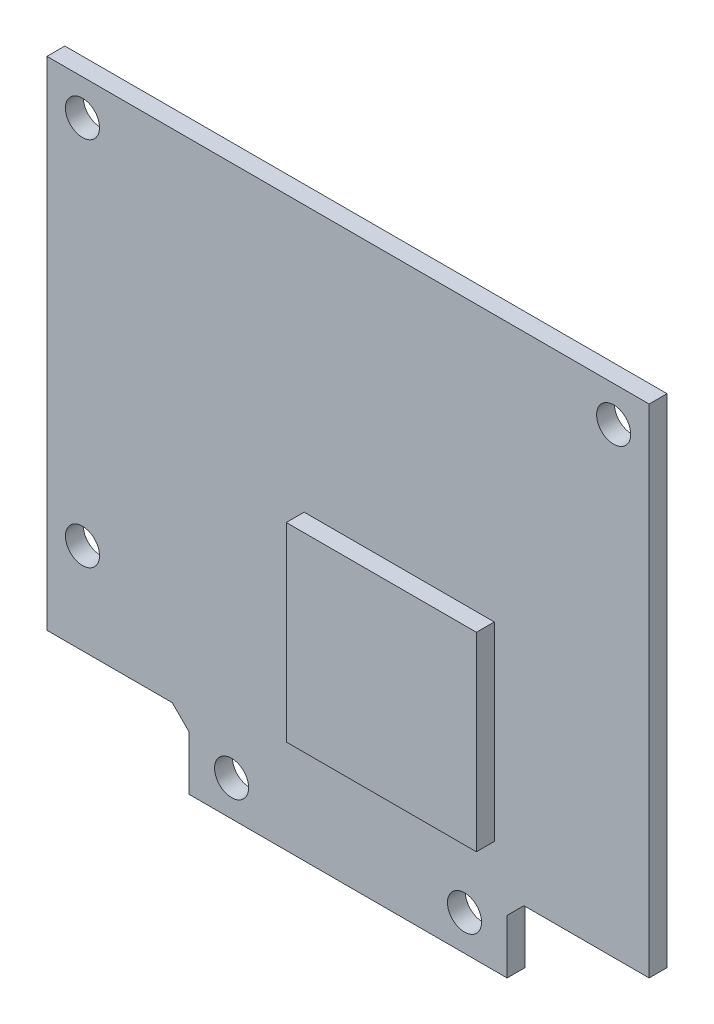
SolidWorks part; units mm, degrees
ref_plane "Plan de face" through (0, 0, 0) normal (0, 0, 1) x (1, 0, 0)
ref_plane "Plan de dessus" through (0, 0, 0) normal (0, 1, 0) x (1, 0, 0)
ref_plane "Plan de droite" through (0, 0, 0) normal (1, 0, 0) x (0, 0, -1)
sketch "PCB_shape" plane through (0, 0, 0) normal (0, 0, 1) x (1, 0, 0)
  line L0 (0, 10.54) -> (0, -40.26) construction
  line L1 (-26.924, 10.54) -> (26.924, 10.54)
  line L2 (-26.924, 10.54) -> (-26.924, -33.91)
  line L3 (-26.924, -33.91) -> (-15.724, -33.91)
  line L4 (26.924, 10.54) -> (26.924, -33.91)
  line L5 (-14.224, -35.41) -> (-14.224, -40.26)
  line L6 (-14.224, -40.26) -> (14.224, -40.26)
  line L7 (14.224, -40.26) -> (14.224, -35.41)
  line L8 (15.724, -33.91) -> (26.924, -33.91)
  line L9 (-26.924, 0) -> (26.924, 0) construction
  line L10 (-15.724, -33.91) -> (-14.224, -35.41)
  line L11 (14.224, -35.41) -> (15.724, -33.91)
  point P6 (14.224, -33.91)
  point P7 (-14.224, -33.91)
  dimension "D1" = 12.7
  dimension "D2" = 50.8
  dimension "D3" = 6.35
  dimension "D4" = 53.848
  dimension "D7" = 10.54
sketch "hole_positions" plane through (0, 0, 0) normal (0, 0, 1) x (1, 0, 0)
  line L0 (-23.749, 7.365) -> (23.749, 7.365) construction
  line L1 (23.749, 7.365) -> (23.749, -25.782) construction
  line L2 (-23.749, 7.365) -> (-23.749, -25.782) construction
  line L3 (-23.749, -25.782) -> (-10.414, -25.782) construction
  line L4 (-10.414, -25.782) -> (-10.414, -37.085) construction
  line L5 (-10.414, -37.085) -> (10.414, -37.085) construction
  line L6 (10.414, -37.085) -> (10.414, -25.782) construction
  line L7 (10.414, -25.782) -> (23.749, -25.782) construction
  line L8 (26.924, 10.54) -> (26.924, -33.91) construction
  line L9 (-26.924, -33.91) -> (-15.724, -33.91) construction
  line L10 (-26.924, 10.54) -> (26.924, 10.54) construction
  line L11 (-14.224, -40.26) -> (14.224, -40.26) construction
  line L13 (0, 7.365) -> (0, -37.085) construction
  line L14 (0, 10.54) -> (0, -40.26) construction
  circle A0 centre (-23.749, 7.365) radius 1.524
  circle A1 centre (-23.749, -25.782) radius 1.524
  circle A2 centre (-10.414, -37.085) radius 1.524
  circle A3 centre (10.414, -37.085) radius 1.524
  circle A4 centre (23.749, 7.365) radius 1.524
  dimension "D6" = 3.048
  dimension "D1" = 3.175
  dimension "D2" = 8.128
  dimension "D3" = 3.175
  dimension "D4" = 3.175
  dimension "D5" = 16.51
sketch "back_components_positions" plane through (0, 0, 0) normal (0, 0, 1) x (1, 0, 0)
  line L0 (-26.924, 10.54) -> (-26.924, -33.91) construction
  line L1 (-13.524, 9.24) -> (-22.524, 9.24)
  line L2 (-13.524, 9.24) -> (-13.524, -11.06)
  line L3 (-13.524, -11.06) -> (-22.524, -11.06)
  line L4 (-22.524, 9.24) -> (-22.524, -11.06)
  line L5 (17.174, 10.54) -> (9.924, 10.54)
  line L6 (17.174, 10.54) -> (17.174, 6.54)
  line L7 (17.174, 6.54) -> (9.924, 6.54)
  line L8 (9.924, 10.54) -> (9.924, 6.54)
  line L9 (22.324, 3.09) -> (18.324, 3.09)
  line L10 (22.324, 3.09) -> (22.324, -4.66)
  line L11 (22.324, -4.66) -> (18.324, -4.66)
  line L12 (18.324, 3.09) -> (18.324, -4.66)
  line L13 (-12.424, -18.91) -> (-17.424, -18.91)
  line L14 (-12.424, -18.91) -> (-12.424, -26.91)
  line L15 (-12.424, -26.91) -> (-17.424, -26.91)
  line L16 (-17.424, -18.91) -> (-17.424, -26.91)
  line L17 (-12.424, -27.56) -> (-17.424, -27.56)
  line L18 (-12.424, -27.56) -> (-12.424, -33.56)
  line L19 (-12.424, -33.56) -> (-17.424, -33.56)
  line L20 (-17.424, -27.56) -> (-17.424, -33.56)
  line L21 (-13.524, 9.24) -> (-22.524, -11.06) construction
  line L22 (-26.924, 10.54) -> (26.924, 10.54) construction
  line L23 (26.924, 10.54) -> (26.924, -33.91) construction
  line L24 (-26.924, -33.91) -> (-15.724, -33.91) construction
  line L25 (-22.524, 9.24) -> (-13.524, -11.06) construction
  line L26 (22.324, 3.09) -> (18.324, -4.66) construction
  line L27 (22.324, -4.66) -> (18.324, 3.09) construction
  line L28 (9.924, 10.54) -> (17.174, 6.54) construction
  line L29 (9.924, 6.54) -> (17.174, 10.54) construction
  line L30 (-12.424, -18.91) -> (-17.424, -26.91) construction
  line L31 (-17.424, -18.91) -> (-12.424, -26.91) construction
  line L32 (-12.424, -27.56) -> (-17.424, -33.56) construction
  line L33 (-17.424, -27.56) -> (-12.424, -33.56) construction
  point P28 (-18.024, -0.91)
  point P29 (20.324, -0.785)
  point P30 (13.549, 8.54)
  point P31 (-14.924, -22.91)
  point P32 (-14.924, -30.56)
  dimension "D1" = 13.4
  dimension "D2" = 9
  dimension "D3" = 20.3
  dimension "D4" = 1.3
  dimension "D5" = 7.25
  dimension "D6" = 17
  dimension "D7" = 4
  dimension "D8" = 5
  dimension "D9" = 8
  dimension "D10" = 15
  dimension "D11" = 14.5
  dimension "D12" = 5
  dimension "D13" = 6
  dimension "D14" = 0.35
  dimension "D15" = 7.75
  dimension "D16" = 8.6
  dimension "D17" = 4
  dimension "D18" = 15.2
sketch "lens_holder_position" plane through (0, 0, 0) normal (0, 0, 1) x (1, 0, 0)
  line L1 (-8, 8) -> (8, 8)
  line L2 (-8, 8) -> (-8, -8)
  line L3 (-8, -8) -> (8, -8)
  line L4 (8, 8) -> (8, -8)
  line L7 (0, 8) -> (0, -8) construction
  dimension "D1" = 16
sketch "led_position" plane through (0, 0, 0) normal (0, 0, 1) x (1, 0, 0)
  line L0 (1.75, -36.66) -> (-1.75, -33.86) construction
  line L1 (1.75, -36.66) -> (-1.75, -36.66)
  line L2 (1.75, -36.66) -> (1.75, -33.86)
  line L3 (1.75, -33.86) -> (-1.75, -33.86)
  line L4 (-1.75, -36.66) -> (-1.75, -33.86)
  line L5 (1.75, -33.86) -> (-1.75, -36.66) construction
  line L7 (0, 10.54) -> (0, -40.26) construction
  line L9 (-14.224, -40.26) -> (14.224, -40.26) construction
  point P4 (0, -35.26)
  dimension "D1" = 2.8
  dimension "D2" = 3.5
  dimension "D3" = 6.4
ref_plane "front_surface" through (0, 0, 1.6) normal (0, 0, 1) x (1, 0, 0)
sketch "Sketch1" plane through (0, 0, 0) normal (0, 0, 1) x (1, 0, 0)
  line L10 (15.724, -33.91) -> (26.924, -33.91)
  line L11 (26.924, -33.91) -> (26.924, 10.54)
  line L12 (26.924, 10.54) -> (-26.924, 10.54)
  line L13 (-26.924, 10.54) -> (-26.924, -33.91)
  line L14 (-26.924, -33.91) -> (-15.724, -33.91)
  line L15 (-15.724, -33.91) -> (-14.224, -35.41)
  line L16 (-14.224, -35.41) -> (-14.224, -40.26)
  line L17 (-14.224, -40.26) -> (14.224, -40.26)
  line L18 (14.224, -40.26) -> (14.224, -35.41)
  line L19 (14.224, -35.41) -> (15.724, -33.91)
  line L20 (15.724, -33.91) -> (26.924, -33.91)
  line L21 (26.924, -33.91) -> (26.924, 10.54)
  line L22 (26.924, 10.54) -> (-26.924, 10.54)
  line L23 (-26.924, 10.54) -> (-26.924, -33.91)
  line L24 (-26.924, -33.91) -> (-15.724, -33.91)
  line L25 (-15.724, -33.91) -> (-14.224, -35.41)
  line L26 (-14.224, -35.41) -> (-14.224, -40.26)
  line L27 (-14.224, -40.26) -> (14.224, -40.26)
  line L28 (14.224, -40.26) -> (14.224, -35.41)
  line L29 (14.224, -35.41) -> (15.724, -33.91)
  dimension "D1" = 0
extrude "Extrude1" add sketch "Sketch1" along normal up to surface (1.6 mm away) up to plane "front_surface"
sketch "Sketch2" plane through (0, 0, 0) normal (0, 0, 1) x (1, 0, 0)
  circle A1 centre (23.749, 7.365) radius 1.524
  circle A2 centre (23.749, 7.365) radius 1.524
  circle A3 centre (10.414, -37.085) radius 1.524
  circle A4 centre (10.414, -37.085) radius 1.524
  circle A5 centre (-10.414, -37.085) radius 1.524
  circle A6 centre (-10.414, -37.085) radius 1.524
  circle A7 centre (-23.749, -25.782) radius 1.524
  circle A8 centre (-23.749, -25.782) radius 1.524
  circle A9 centre (-23.749, 7.365) radius 1.524
  circle A10 centre (-23.749, 7.365) radius 1.524
  dimension "D1" = 0
  dimension "D2" = 0
  dimension "D3" = 0
  dimension "D4" = 0
  dimension "D5" = 0
extrude "Extrude2" cut sketch "Sketch2" along normal through all
sketch "Sketch4" plane through (0, 0, 1.6) normal (0, 0, 1) x (1, 0, 0)
  line L0 (-14.224, -40.26) -> (14.224, -40.26) construction
  line L1 (-3.924, -13.26) -> (13.076, -13.26)
  line L2 (-3.924, -13.26) -> (-3.924, -30.26)
  line L3 (-3.924, -30.26) -> (13.076, -30.26)
  line L4 (13.076, -13.26) -> (13.076, -30.26)
  line L5 (-26.924, 10.54) -> (-26.924, -33.91) construction
  dimension "D1" = 17
  dimension "D2" = 27
  dimension "D3" = 40
extrude "Extrude3" add sketch "Sketch4" along normal blind 1.6
